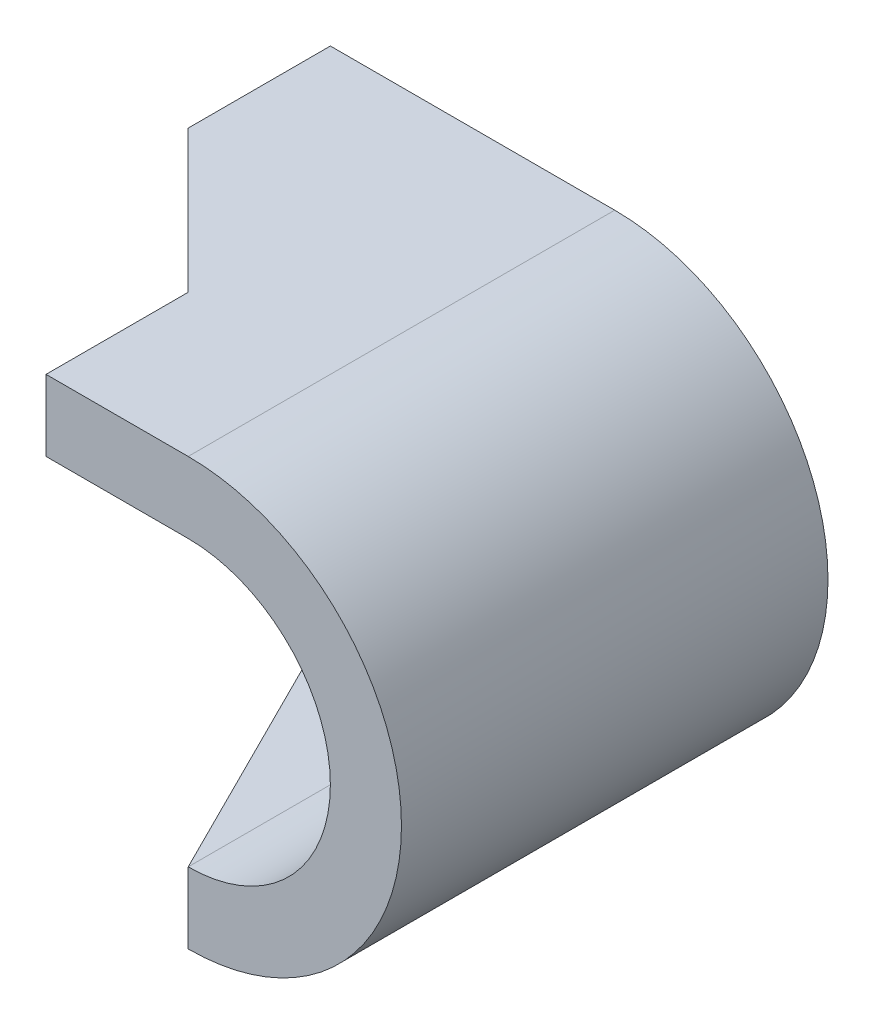
SolidWorks part; units mm, degrees
ref_plane "Front Plane" through (0, 0, 0) normal (0, 0, 1) x (1, 0, 0)
ref_plane "Top Plane" through (0, 0, 0) normal (0, 1, 0) x (1, 0, 0)
ref_plane "Right Plane" through (0, 0, 0) normal (1, 0, 0) x (0, 0, -1)
sketch "Sketch2" plane through (0, 0, 0) normal (0, 0, 1) x (1, 0, 0)
  line L0 (0, 2) -> (-4, 2)
  line L1 (-4, 2) -> (-4, 3)
  line L2 (-4, 3) -> (0, 3)
  line L3 (0, -2) -> (-2, -2)
  line L4 (-2, -2) -> (-2, -3)
  line L5 (-2, -3) -> (0, -3)
  arc A0 (0, 2) -> (0, -2) centre (0, 0) cw
  arc A1 (0, 3) -> (0, -3) centre (0, 0) cw
  dimension "D1" = 2
  dimension "D2" = 3
  dimension "D3" = 1
  dimension "D4" = 4
  dimension "D5" = 1
  dimension "D6" = 2
extrude "Boss-Extrude1" add sketch "Sketch2" along normal blind 6
sketch "Sketch3" plane through (0, 2, 0) normal (0, -1, 0) x (1, 0, 0)
  line L0 (-2, 6) -> (-2, 4)
  line L1 (-2, 6) -> (-2, 0) construction
  line L2 (-2, 4) -> (-4, 2)
  line L3 (-4, 6) -> (-4, 0) construction
  line L4 (-4, 2) -> (-4, 6)
  line L5 (-4, 6) -> (-2, 6)
  dimension "D1" = 2
  dimension "D2" = 2
extrude "Cut-Extrude1" cut sketch "Sketch3" against normal blind 6
sketch "Sketch4" plane through (0, -3, 0) normal (0, -1, 0) x (1, 0, 0)
  line L0 (0, 6) -> (-2, 2)
  line L1 (-2, 6) -> (-2, 0) construction
  line L2 (-2, 2) -> (-2, 6)
  line L3 (-2, 6) -> (0, 6)
  dimension "D1" = 2
extrude "Cut-Extrude2" cut sketch "Sketch4" against normal blind 1
